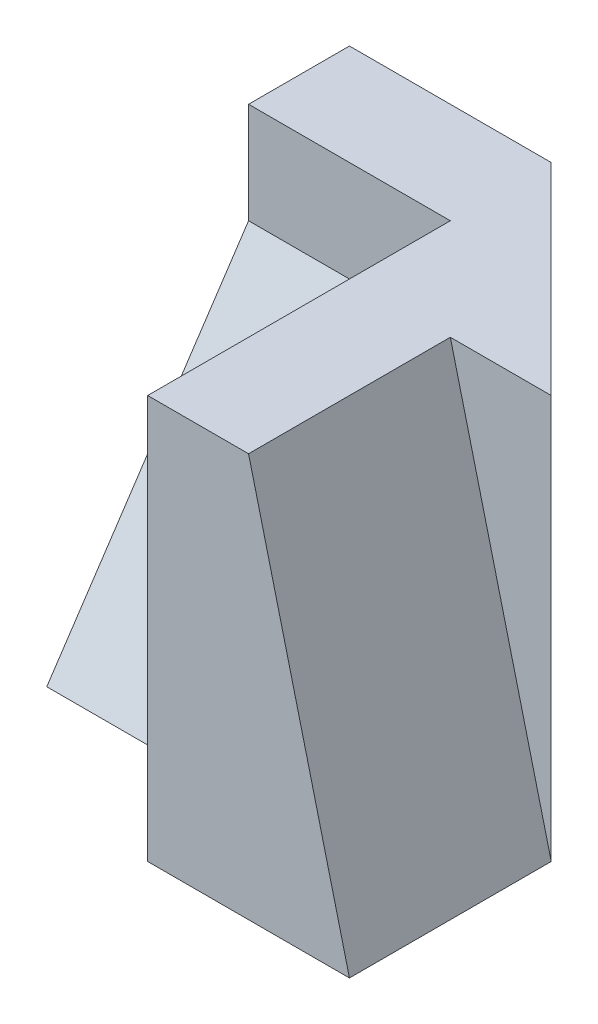
SolidWorks part; units mm, degrees
ref_plane "Front Plane" through (0, 0, 0) normal (0, 0, 1) x (1, 0, 0)
ref_plane "Top Plane" through (0, 0, 0) normal (0, 1, 0) x (1, 0, 0)
ref_plane "Right Plane" through (0, 0, 0) normal (1, 0, 0) x (0, 0, -1)
sketch "Sketch1" plane through (0, 0, 0) normal (0, 1, 0) x (1, 0, 0)
  line L0 (0, 0) -> (2, 0)
  line L1 (2, 0) -> (2, 2)
  line L2 (2, 2) -> (0, 4)
  line L3 (0, 4) -> (-2, 4)
  line L4 (-2, 4) -> (-2, 1)
  line L5 (-2, 1) -> (0, 1)
  line L6 (0, 1) -> (0, 0)
  dimension "D1" = 1
  dimension "D2" = 2
  dimension "D3" = 3
  dimension "D4" = 2
  dimension "D5" = 2
  dimension "D6" = 2
extrude "Boss-Extrude1" add sketch "Sketch1" along normal blind 4
sketch "Sketch3" plane through (0, 0, 0) normal (0, 0, 1) x (1, 0, 0)
  line L0 (1, 4) -> (2, 0)
  line L1 (0, 4) -> (2, 4) construction
  line L2 (2, 0) -> (2, 4)
  line L3 (2, 4) -> (1, 4)
extrude "Cut-Extrude2" cut sketch "Sketch3" against normal blind 2
sketch "Sketch4" plane through (-2, 0, 0) normal (-1, 0, 0) x (0, 0, 1)
  line L0 (-1, 4) -> (-3, 4)
  line L1 (-4, 4) -> (-1, 4) construction
  line L2 (-3, 4) -> (-3, 3)
  line L3 (-3, 3) -> (-1, 0)
  line L4 (-1, 0) -> (-1, 4)
  dimension "D1" = 2
  dimension "D2" = 1
extrude "Cut-Extrude3" cut sketch "Sketch4" against normal blind 2
